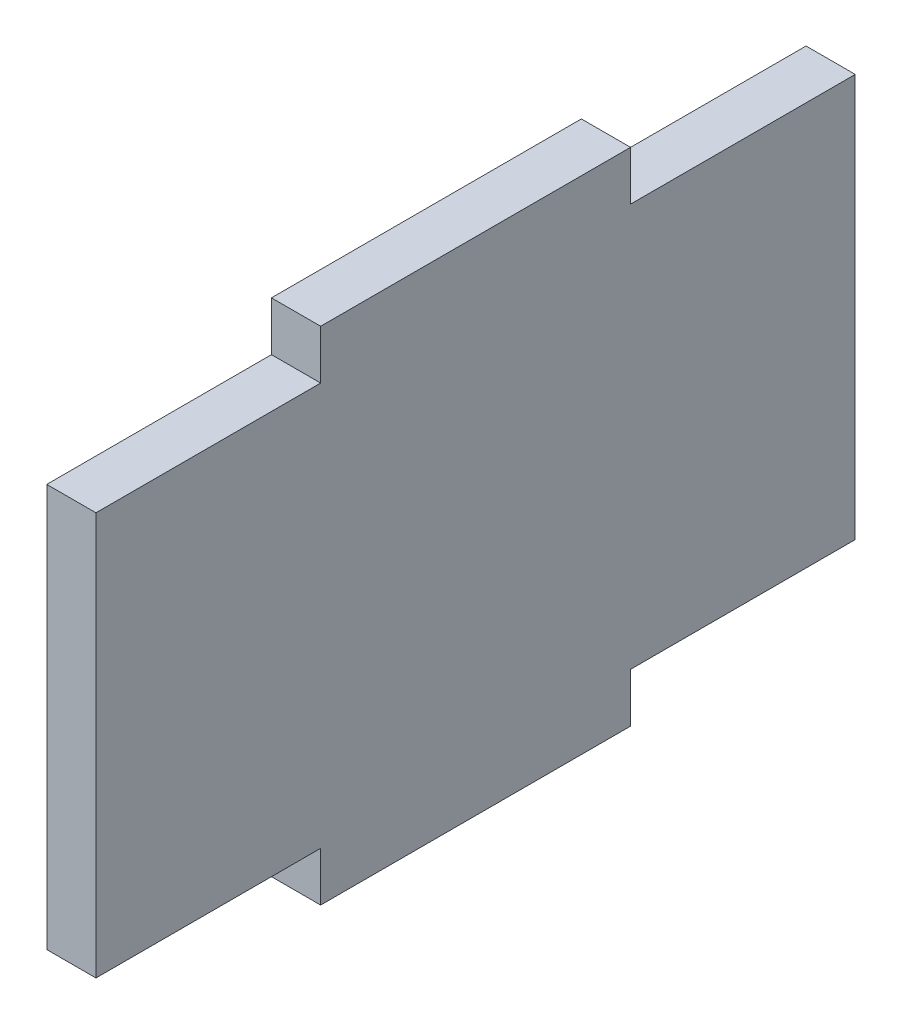
SolidWorks part; units mm, degrees
ref_plane "Front Plane" through (0, 0, 0) normal (0, 0, 1) x (1, 0, 0)
ref_plane "Top Plane" through (0, 0, 0) normal (0, 1, 0) x (1, 0, 0)
ref_plane "Right Plane" through (0, 0, 0) normal (1, 0, 0) x (0, 0, -1)
sketch "Sketch1" plane through (0, 0, 0) normal (1, 0, 0) x (0, 0, -1)
  line L0 (0, 0) -> (-24.5, 0) construction
  line L1 (-24.5, -16.175) -> (24.5, -16.175)
  line L2 (-24.5, -16.175) -> (-24.5, 16.175)
  line L3 (-24.5, 16.175) -> (24.5, 16.175)
  line L4 (24.5, -16.175) -> (24.5, 16.175)
  line L5 (-24.5, -16.175) -> (24.5, 16.175) construction
  line L6 (-24.5, 16.175) -> (24.5, -16.175) construction
  line L7 (-10, 19.35) -> (10, 19.35)
  line L8 (-10, 19.35) -> (-10, 13)
  line L9 (-24.5, 13) -> (24.5, 13)
  line L10 (10, 19.35) -> (10, 13)
  line L11 (-10, 19.35) -> (10, 13) construction
  line L12 (-10, 13) -> (10, 19.35) construction
  line L13 (-10, -13) -> (10, -19.35) construction
  line L14 (-10, -19.35) -> (10, -13) construction
  line L15 (10, -19.35) -> (10, -13)
  line L16 (-24.5, -13) -> (24.5, -13)
  line L17 (-10, -19.35) -> (-10, -13)
  line L18 (-10, -19.35) -> (10, -19.35)
  point P0 (0, 0)
  point P6 (0, 16.175)
  point P17 (0, -16.175)
  dimension "D1" = 49
  dimension "D2" = 3.175
  dimension "D3" = 20
  dimension "D4" = 13
extrude "Boss-Extrude1" add sketch "Sketch1" along normal blind 3.175 contours L10 L3 L8 L9 | L2 L16 L4 L9 | L17 L1 L15 L16
